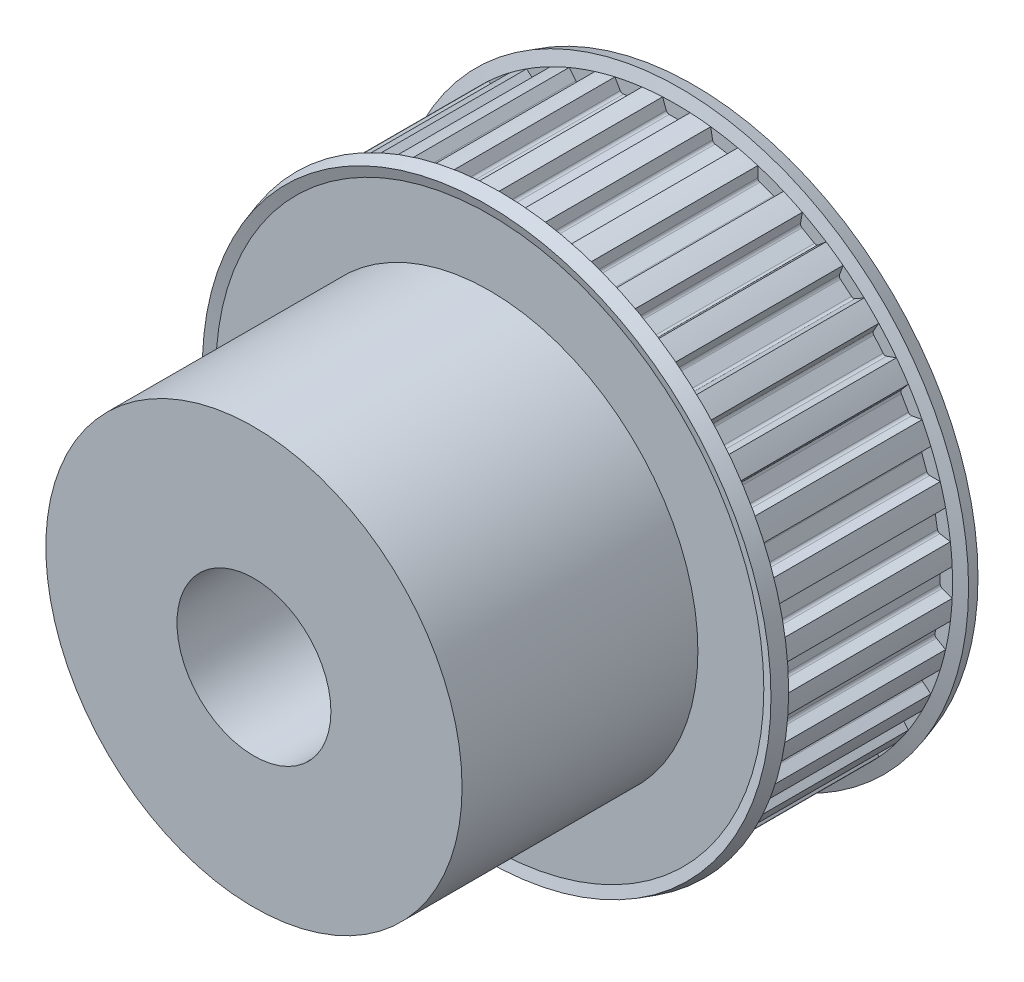
SolidWorks part; units mm, degrees
material "6061 Alloy"
ref_plane "Plane1" through (0, 0, 0) normal (0, 0, 1) x (1, 0, 0)
ref_plane "Plane2" through (0, 0, 0) normal (0, 1, 0) x (1, 0, 0)
ref_plane "Plane3" through (0, 0, 0) normal (1, 0, 0) x (0, 0, -1)
sketch "Clipboard" plane through (0, 0, 0) normal (0, 0, 1) x (1, 0, 0)
  line L0 (0, 0) -> (6.604, 0)
  line L1 (0, 0) -> (14.0966, 10.2418)
  line L2 (0, 0) -> (14.0966, -10.2418)
  dimension "Overall_len" = 17.4244
  dimension "T_dim" = 6.604
  dimension "OAL" = 17.4244
  dimension "Show_grvs" = 36
  dimension "Num_grvs" = 36
sketch "Sketch1" plane through (0, 0, 0) normal (0, 0, 1) x (1, 0, 0)
  circle A0 centre (0, 0) radius 11.3919
  dimension "Outside_dia" = 22.7838
extrude "BasePulley" add sketch "Sketch1" against normal blind 7.112
sketch "Sketch2" plane through (0, 0, 0) normal (1, 0, 0) x (0, 0, -1)
  line L0 (7.112, 11.3919) -> (7.2673, 11.8999)
  line L1 (7.2673, 11.8999) -> (7.826, 11.7291)
  line L2 (3.556, 0) -> (3.556, 66.675) construction
  line L3 (7.826, 11.7291) -> (7.6962, 11.3046)
  line L4 (7.6962, 11.3046) -> (7.6962, 0)
  line L5 (0, 11.3919) -> (-0.1553, 11.8999)
  line L6 (7.112, -11.3919) -> (7.112, 11.3919) construction
  line L7 (-0.1553, 11.8999) -> (-0.714, 11.7291)
  line L8 (-0.714, 11.7291) -> (-0.5842, 11.3046)
  line L9 (-0.5842, 11.3046) -> (-0.5842, 0)
  line L10 (7.112, 11.3919) -> (0, 11.3919)
  line L11 (0, 0) -> (38.2092, 0) construction
  line L12 (7.112, 0) -> (0, 0) construction
  line L13 (-0.5842, 0) -> (7.6962, 0)
  dimension "D1" = 3.556
  dimension "Flange_ang" = 17
  dimension "Flange_thickness" = 0.5842
  dimension "D2" = 11.3919
  dimension "Flange_ht" = 0.508
  dimension "D3" = 0.5842
revolve "Flange" add sketch "Sketch2" angle 360 about L11
ref_plane "Plane4" through (0, 0, -3.556) normal (0, 0, 1) x (1, 0, 0)
sketch "Sketch3" plane through (0, 0, -3.556) normal (0, 0, 1) x (1, 0, 0)
  line L0 (-0.5715, 11.3919) -> (-0.5715, 36.7919)
  line L1 (0.5715, 11.3919) -> (0.5715, 36.7919)
  line L2 (0, 0) -> (0, 11.3919) construction
  line L3 (-0.5715, 11.3919) -> (0.5715, 11.3919) construction
  line L4 (-0.2977, 10.8839) -> (0.2977, 10.8839)
  line L5 (0.5715, 11.3919) -> (0.417, 10.9675)
  line L6 (-0.5715, 11.3919) -> (-0.417, 10.9675)
  line L7 (0.5715, 36.7919) -> (-0.5715, 36.7919)
  arc A0 (0.2977, 10.8839) -> (0.417, 10.9675) centre (0.2977, 11.0109) ccw
  arc A2 (-0.417, 10.9675) -> (-0.2977, 10.8839) centre (-0.2977, 11.0109) ccw
  dimension "Grv_rad_bot" = 0.127
  dimension "D4" = 25.4
  dimension "D1" = 11.3919
  dimension "Grv_ang" = 40
  dimension "Grv_width" = 1.143
  dimension "D3" = 20
  dimension "Grv_depth" = 0.508
extrude "Groove" cut sketch "Sketch3" against normal mid plane 7.112
pattern_circular "Grooves" count 36 every 10 about axis through (0, 0, -7.112) along (0, 0, 1) of "Groove"
sketch "Sketch4" plane through (0, 0, 0) normal (1, 0, 0) x (0, 0, -1)
  line L0 (0, 0) -> (47.6781, 0) construction
  line L1 (7.112, 0) -> (0, 0) construction
  line L2 (0, 0) -> (-10.3124, 0)
  line L3 (-10.3124, 0) -> (-10.3124, 8.5852)
  line L4 (-10.3124, 8.5852) -> (0, 8.5852)
  line L5 (0, 8.5852) -> (0, 0)
  line L6 (-10.3124, -8.5852) -> (0, -8.5852) construction
  dimension "Hub_dia" = 17.1704
  dimension "Hub_depth" = 10.3124
revolve "BaseHub" add sketch "Sketch4" angle 360 about L0
sketch "BorSke" plane through (0, 0, 10.3124) normal (0, 0, 1) x (1, 0, 0)
  circle A0 centre (0, 0) radius 3.175
  dimension "Diameter" = 6.35
extrude "Bore" cut sketch "BorSke" against normal through all
sketch "KeySke" plane through (0, 0, 10.3124) normal (0, 0, 1) x (1, 0, 0)
  line L0 (0.127, 3.429) -> (0.127, 0)
  line L1 (0.127, 3.429) -> (-0.127, 3.429)
  line L2 (-0.127, 3.429) -> (-0.127, 0)
  line L3 (-0.127, 0) -> (0.127, 0)
  line L4 (0, 31.75) -> (0, -3.175) construction
  dimension "Width" = 0.254
  dimension "Offset" = 3.429
extrude "Keyway" [suppressed] cut sketch "KeySke" against normal through all
pattern_circular "Keyway2" [suppressed] count 2 every 90
equation "\"D1@Plane4\" = \"Width@BasePulley\" / 2"
equation "\"D1@Groove\" = \"Width@BasePulley\""
equation "\"D1@Sketch3\" = \"Outside_dia@Sketch1\" / 2"
equation "\"D1@Sketch2\" = \"Width@BasePulley\" / 2"
equation "\"D2@Sketch2\" = \"Outside_dia@Sketch1\" / 2"
equation "\"D3@Sketch2\" = \"Flange_thickness@Sketch2\""
equation "\"Num_grvs@Clipboard\" = int( \"Num_grvs@Clipboard\" )"
equation "\"Show_grvs@Clipboard\" = int( \"Show_grvs@Clipboard\" )"
equation "\"Show_grvs@Clipboard\" = ((sgn( \"Show_grvs@Clipboard\" - \"Num_grvs@Clipboard\" )-1)*( \"Show_grvs@Clipboard\" - \"Num_grvs@Clipboard\" ))/-2+ \"Num_grvs@Clipboard\""
equation "\"Show_grvs@Clipboard\" = ((sgn( \"Show_grvs@Clipboard\" - 1.0)+1)*( \"Show_grvs@Clipboard\" - 1.0))/2 +1.0"
equation "\"Angle@Grooves\" = 360.0 / \"Num_grvs@Clipboard\""
equation "\"Num_grvs@Grooves\" =  \"Show_grvs@Clipboard\""
equation "\"Offset@KeySke\" = \"T_dim@Clipboard\" - \"Diameter@BorSke\" / 2.0"
equation "\"OAL@Clipboard\" = \"Overall_len@Clipboard\""
equation "\"Hub_depth@Sketch4\" = \"OAL@Clipboard\" - \"Width@BasePulley\""
